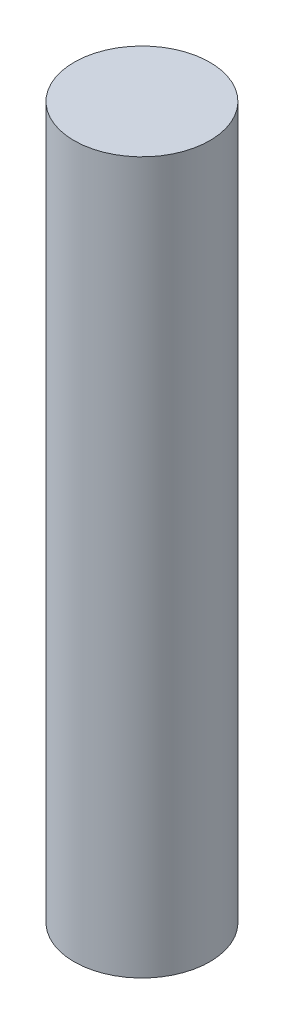
SolidWorks part; units mm, degrees
ref_plane "Front Plane" through (0, 0, 0) normal (0, 0, 1) x (1, 0, 0)
ref_plane "Top Plane" through (0, 0, 0) normal (0, 1, 0) x (1, 0, 0)
ref_plane "Right Plane" through (0, 0, 0) normal (1, 0, 0) x (0, 0, -1)
sketch "Sketch1" plane through (0, 0, 0) normal (0, 1, 0) x (1, 0, 0)
  circle A0 centre (0, 0) radius 21
extrude "Boss-Extrude1" add sketch "Sketch1" along normal blind 220
